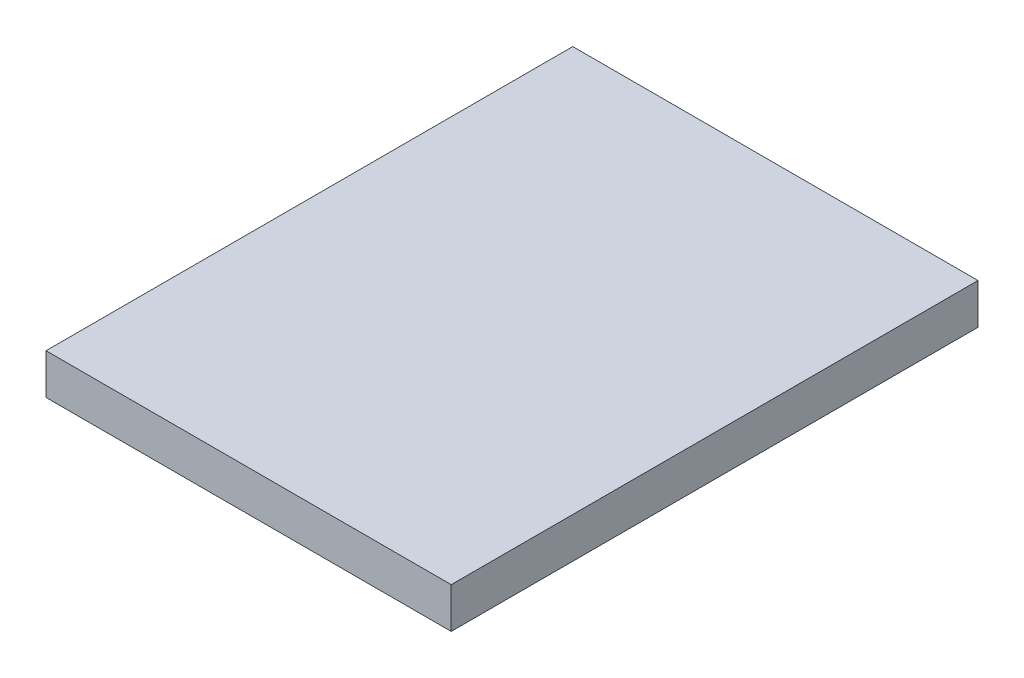
SolidWorks part; units mm, degrees
ref_plane "Front Plane" through (0, 0, 0) normal (0, 0, 1) x (1, 0, 0)
ref_plane "Top Plane" through (0, 0, 0) normal (0, 1, 0) x (1, 0, 0)
ref_plane "Right Plane" through (0, 0, 0) normal (1, 0, 0) x (0, 0, -1)
sketch "Sketch1" plane through (0, 0, 0) normal (0, 1, 0) x (1, 0, 0)
  line L1 (0, 0) -> (63.5, 0)
  line L2 (0, 0) -> (0, 82.55)
  line L3 (0, 82.55) -> (63.5, 82.55)
  line L4 (63.5, 0) -> (63.5, 82.55)
  point P13 (16.51, 49.2267)
  dimension "D1" = 82.55
  dimension "D2" = 63.5
extrude "Boss-Extrude1" add sketch "Sketch1" along normal blind 6.35
